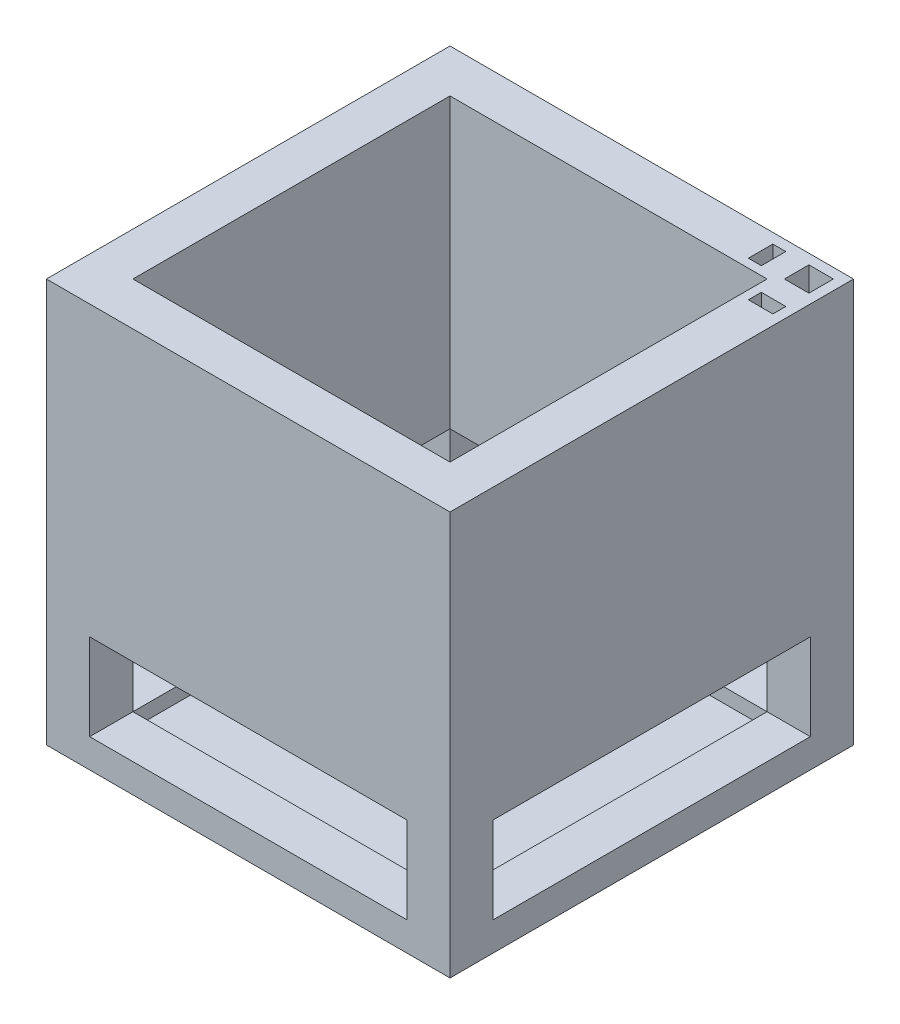
SolidWorks part; units mm, degrees
ref_plane "Front Plane" through (0, 0, 0) normal (0, 0, 1) x (1, 0, 0)
ref_plane "Top Plane" through (0, 0, 0) normal (0, 1, 0) x (1, 0, 0)
ref_plane "Right Plane" through (0, 0, 0) normal (1, 0, 0) x (0, 0, -1)
sketch "Sketch1" plane through (0, 0, 0) normal (0, 1, 0) x (1, 0, 0)
  line L1 (-70, 70) -> (70, 70)
  line L2 (-70, 70) -> (-70, -70)
  line L3 (-70, -70) -> (70, -70)
  line L4 (70, 70) -> (70, -70)
  line L5 (-70, 70) -> (70, -70) construction
  line L6 (-70, -70) -> (70, 70) construction
  point P0 (0, 0)
  dimension "D1" = 140
  dimension "D2" = 140
extrude "Boss-Extrude1" add sketch "Sketch1" along normal blind 140
sketch "Sketch3" plane through (0, 0, 0) normal (0, 1, 0) x (1, 0, 0)
  line L1 (-55, 55) -> (55, 55)
  line L2 (-55, 55) -> (-55, -55)
  line L3 (-55, -55) -> (55, -55)
  line L4 (55, 55) -> (55, -55)
  line L5 (-55, 55) -> (55, -55) construction
  line L6 (-55, -55) -> (55, 55) construction
  point P0 (0, 0)
  dimension "D1" = 110
  dimension "D2" = 110
extrude "Cut-Extrude1" cut sketch "Sketch3" along normal blind 140
sketch "Sketch4" plane through (0, 0, 0) normal (0, 1, 0) x (1, 0, 0)
  line L1 (-70, 70) -> (70, 70)
  line L2 (-70, 70) -> (-70, -70)
  line L3 (-70, -70) -> (70, -70)
  line L4 (70, 70) -> (70, -70)
  line L5 (-70, 70) -> (70, -70) construction
  line L6 (-70, -70) -> (70, 70) construction
  point P0 (0, 0)
extrude "Boss-Extrude2" add sketch "Sketch4" along normal blind 5
sketch "Sketch8" plane through (0, 0, 0) normal (0, 1, 0) x (1, 0, 0)
  line L0 (70, -70) -> (70, 70) construction
  line L1 (58, 66.5) -> (66.5, 66.5)
  line L2 (58, 66.5) -> (58, 58)
  line L3 (58, 58) -> (66.5, 58)
  line L4 (66.5, 66.5) -> (66.5, 58)
  line L5 (58, 66.5) -> (66.5, 58) construction
  line L6 (58, 58) -> (66.5, 66.5) construction
  line L7 (70, 70) -> (-70, 70) construction
  line L8 (55, -55) -> (55, 55) construction
  point P0 (62.25, 62.25)
  dimension "D1" = 3.5
  dimension "D2" = 8.5
  dimension "D3" = 8.5
  dimension "D4" = 3.5
  dimension "D5" = 3
extrude "Cut-Extrude4" cut sketch "Sketch8" along normal blind 140
sketch "Sketch9" plane through (0, 0, 0) normal (0, 1, 0) x (1, 0, 0)
  line L1 (55, 55) -> (46.5, 55)
  line L2 (55, 55) -> (55, 46.5)
  line L3 (55, 46.5) -> (46.5, 46.5)
  line L4 (46.5, 55) -> (46.5, 46.5)
  dimension "D1" = 8.5
  dimension "D2" = 8.5
sketch "Sketch10" plane through (0, 0, 0) normal (0, 1, 0) x (1, 0, 0)
  line L1 (66.5, 66.5) -> (46.5, 66.5)
  line L2 (66.5, 66.5) -> (66.5, 46.5)
  line L3 (66.5, 46.5) -> (46.5, 46.5)
  line L4 (46.5, 66.5) -> (46.5, 46.5)
extrude "Cut-Extrude5" cut sketch "Sketch10" along normal blind 100
sketch "Sketch11" plane through (0, 0, 0) normal (0, 1, 0) x (1, 0, 0)
  line L2 (70, 70) -> (46.5, 70)
  line L3 (70, 70) -> (70, 46.5)
  line L4 (70, 46.5) -> (46.5, 46.5)
  line L5 (46.5, 70) -> (46.5, 46.5)
sketch "Sketch12" plane through (0, 0, 0) normal (0, 1, 0) x (1, 0, 0)
  line L2 (70, 70) -> (41.352, 70)
  line L3 (70, 70) -> (70, 41.2659)
  line L4 (70, 41.2659) -> (41.352, 41.2659)
  line L5 (41.352, 70) -> (41.352, 41.2659)
extrude "Boss-Extrude4" add sketch "Sketch12" along normal blind 5
sketch "Sketch14" plane through (0, 0, 0) normal (0, 1, 0) x (1, 0, 0)
  line L2 (70, 70) -> (55, 70)
  line L3 (70, 70) -> (70, 55)
  line L4 (70, 55) -> (55, 55)
  line L5 (55, 70) -> (55, 55)
sketch "Sketch18" plane through (0, 0, 0) normal (0, 1, 0) x (1, 0, 0)
  line L1 (70, 70) -> (46.5, 70)
  line L2 (70, 70) -> (70, 55)
  line L3 (70, 55) -> (46.5, 55)
  line L4 (46.5, 70) -> (46.5, 55)
extrude "Boss-Extrude6" add sketch "Sketch18" along normal blind 70
sketch "Sketch19" plane through (0, 0, 0) normal (0, 1, 0) x (1, 0, 0)
  line L0 (55, -55) -> (55, 55) construction
  line L1 (70, 70) -> (55, 70)
  line L2 (70, 70) -> (70, 43.5058)
  line L3 (70, 43.5058) -> (55, 43.5058)
  line L4 (55, 70) -> (55, 43.5058)
extrude "Boss-Extrude7" add sketch "Sketch19" along normal blind 70
sketch "Sketch24" plane through (0, 0, 0) normal (1, 0, 0) x (0, 0, -1)
  line L0 (-70, 0) -> (70, 0) construction
  line L1 (55, 40) -> (-55, 40)
  line L2 (55, 40) -> (55, 10)
  line L3 (55, 10) -> (-55, 10)
  line L4 (-55, 40) -> (-55, 10)
  line L5 (70, 140) -> (70, 0) construction
  line L6 (-70, 140) -> (-70, 0) construction
  dimension "D1" = 30
  dimension "D2" = 10
  dimension "D3" = 15
  dimension "D4" = 15
  dimension "D5" = 110
extrude "Cut-Extrude8" cut sketch "Sketch24" against normal blind 70 and the other way blind 70
sketch "Sketch25" plane through (0, 0, 0) normal (0, 0, 1) x (1, 0, 0)
  line L0 (70, 140) -> (70, 0) construction
  line L1 (-55, 40) -> (55, 40)
  line L2 (-55, 40) -> (-55, 10)
  line L3 (-55, 10) -> (55, 10)
  line L4 (55, 40) -> (55, 10)
  line L5 (-70, 140) -> (-70, 0) construction
  line L6 (-70, 0) -> (70, 0) construction
  dimension "D1" = 15
  dimension "D2" = 15
  dimension "D3" = 10
  dimension "D4" = 30
  dimension "D5" = 110
extrude "Cut-Extrude9" cut sketch "Sketch25" against normal blind 70 and the other way blind 70
sketch "Sketch26" plane through (0, 0, 0) normal (0, 1, 0) x (1, 0, 0)
  line L0 (70, 70) -> (70, 55) construction
  line L1 (45.5, 66.5) -> (50, 66.5)
  line L2 (45.5, 66.5) -> (45.5, 58)
  line L3 (45.5, 58) -> (50, 58)
  line L4 (50, 66.5) -> (50, 58)
  line L5 (58, 50) -> (66.5, 50)
  line L6 (58, 50) -> (58, 45.5)
  line L7 (58, 45.5) -> (66.5, 45.5)
  line L8 (66.5, 50) -> (66.5, 45.5)
  line L9 (70, 70) -> (55, 70) construction
  line L10 (70, 70) -> (-70, 70) construction
  line L11 (70, -70) -> (70, 70) construction
  line L12 (55, -55) -> (55, 55) construction
  dimension "D1" = 20
  dimension "D2" = 20
  dimension "D3" = 8.5
  dimension "D4" = 8.5
  dimension "D5" = 3.5
  dimension "D6" = 3.5
  dimension "D7" = 4.5
  dimension "D8" = 4.5
  dimension "D9" = 3
sketch "Sketch27" plane through (0, 0, 0) normal (0, 1, 0) x (1, 0, 0)
  line L1 (45.5, 66.5) -> (50.0292, 66.5)
  line L2 (45.5, 66.5) -> (45.5, -73.5775)
  line L3 (45.5, -73.5775) -> (50.0292, -73.5775)
  line L4 (50.0292, 66.5) -> (50.0292, -73.5775)
  line L5 (45.5, 66.5) -> (86.7748, 66.5)
  line L6 (45.5, 66.5) -> (50.0292, 66.5)
  line L7 (45.5, 66.5) -> (45.5, 76.6827)
  line L8 (45.5, 76.6827) -> (50.0292, 76.6827)
  line L9 (50.0292, 66.5) -> (50.0292, 76.6827)
  line L10 (45.5, 66.5) -> (45.5, 57.8786)
  line L11 (45.5, 57.8786) -> (86.7748, 57.8786)
  line L12 (86.7748, 66.5) -> (86.7748, 57.8786)
  line L13 (86.7748, 57.8786) -> (-10.5234, 57.8786)
  line L14 (86.7748, 57.8786) -> (86.7748, 66.5)
  line L15 (86.7748, 66.5) -> (-10.5234, 66.5)
  line L16 (-10.5234, 57.8786) -> (-10.5234, 66.5)
  line L17 (-10.5234, 66.5) -> (-80.6401, 66.5)
  line L18 (-10.5234, 66.5) -> (-10.5234, 57.8786)
  line L19 (-10.5234, 57.8786) -> (-80.6401, 57.8786)
  line L20 (-80.6401, 66.5) -> (-80.6401, 57.8786)
sketch "Sketch28" plane through (0, 0, 0) normal (0, 0, 1) x (1, 0, 0)
  line L0 (70, 140) -> (-70, 140) construction
  line L1 (50, 140) -> (45.5, 140)
  line L2 (50, 140) -> (50, 135.5)
  line L3 (50, 135.5) -> (45.5, 135.5)
  line L4 (45.5, 140) -> (45.5, 135.5)
  line L5 (70, 140) -> (70, 0) construction
  dimension "D1" = 20
  dimension "D2" = 4.5
  dimension "D3" = 4.5
extrude "Cut-Extrude10" cut sketch "Sketch28" against normal up to vertex (66.5 mm away) up to point (45.5, 0, -66.5)
sketch "Sketch29" plane through (0, 0, 0) normal (1, 0, 0) x (0, 0, -1)
  line L1 (-70, 140) -> (70, 140) construction
  line L2 (50, 140) -> (45.5, 140)
  line L3 (50, 140) -> (50, 135.5)
  line L4 (50, 135.5) -> (45.5, 135.5)
  line L5 (45.5, 140) -> (45.5, 135.5)
  line L7 (70, 140) -> (70, 0) construction
  dimension "D1" = 20
  dimension "D2" = 4.5
  dimension "D3" = 4.5
extrude "Cut-Extrude11" cut sketch "Sketch29" along normal blind 66.5
sketch "Sketch30" plane through (0, 0, 0) normal (0, 0, 1) x (1, 0, 0)
  line L0 (70, 140) -> (-70, 140) construction
  line L1 (50, 140) -> (45.5, 140)
  line L2 (50, 140) -> (50, 135.5)
  line L3 (50, 135.5) -> (45.5, 135.5)
  line L4 (45.5, 140) -> (45.5, 135.5)
  line L5 (70, 140) -> (70, 0) construction
  dimension "D1" = 4.5
  dimension "D2" = 4.5
  dimension "D3" = 20
extrude "Boss-Extrude8" add sketch "Sketch30" against normal blind 58
sketch "Sketch32" plane through (0, 0, 0) normal (1, 0, 0) x (0, 0, -1)
  line L0 (-70, 140) -> (70, 140) construction
  line L1 (45.5, 140) -> (50, 140)
  line L2 (45.5, 140) -> (45.5, 135.5)
  line L3 (45.5, 135.5) -> (50, 135.5)
  line L4 (50, 140) -> (50, 135.5)
  line L5 (70, 140) -> (70, 0) construction
  dimension "D1" = 4.5
  dimension "D2" = 4.5
  dimension "D3" = 20
extrude "Boss-Extrude9" add sketch "Sketch32" along normal blind 58
sketch "Sketch34" plane through (0, 0, 0) normal (0, 1, 0) x (1, 0, 0)
  line L1 (55, 55) -> (-55, 55) construction
  line L2 (-3.0428, 55) -> (55, 55)
  line L3 (-3.0428, 55) -> (-3.0428, 0)
  line L4 (-3.0428, 0) -> (55, 0)
  line L5 (55, 55) -> (55, 0)
  line L6 (55, -55) -> (55, 45.5) construction
extrude "Cut-Extrude20" cut sketch "Sketch34" along normal blind 140
sketch "Sketch35" plane through (0, 0, 0) normal (0, 1, 0) x (1, 0, 0)
  line L1 (60.2811, 60.7105) -> (-5.4499, 60.7105)
  line L2 (60.2811, 60.7105) -> (60.2811, -2.9837)
  line L3 (60.2811, -2.9837) -> (-5.4499, -2.9837)
  line L4 (-5.4499, 60.7105) -> (-5.4499, -2.9837)
extrude "Boss-Extrude10" add sketch "Sketch35" along normal blind 5
